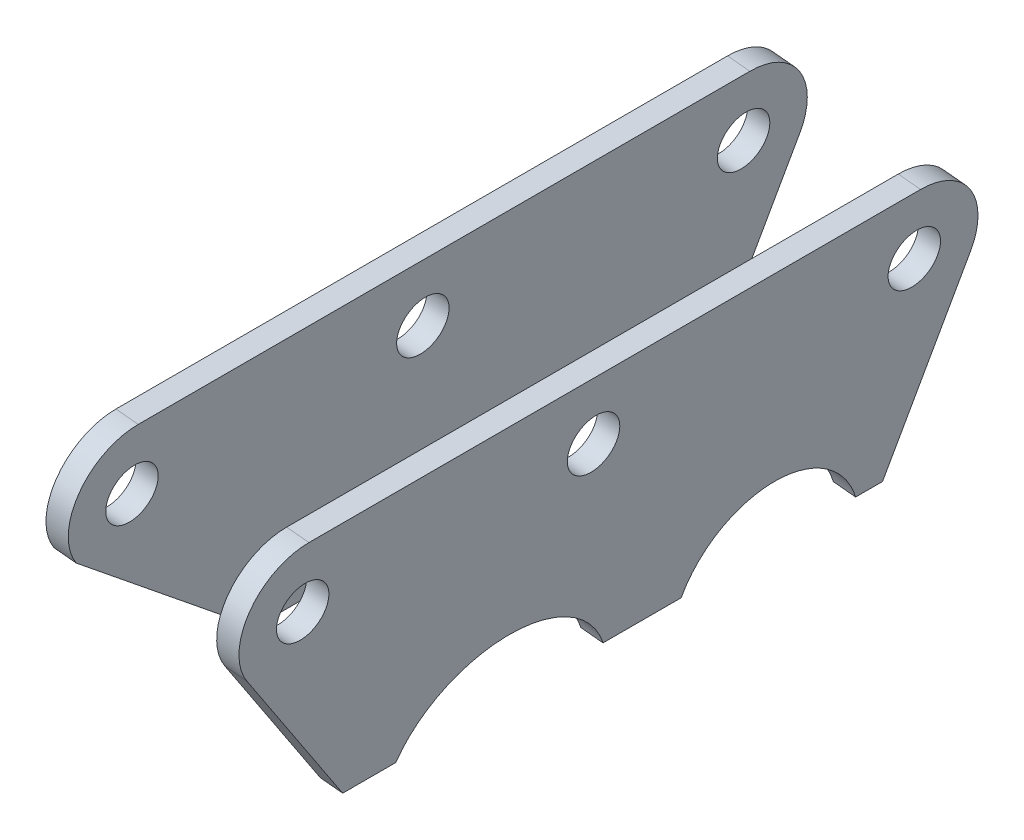
SolidWorks part; units mm, degrees
material "1.0545 (S355N)"
ref_plane "Płaszczyzna XY" through (0, 0, 0) normal (0, 0, 1) x (1, 0, 0)
ref_plane "Płaszczyzna XZ" through (0, 0, 0) normal (0, 1, 0) x (1, 0, 0)
ref_plane "Płaszczyzna YZ" through (0, 0, 0) normal (1, 0, 0) x (0, 0, -1)
ref_plane "Płaszczyzna1" through (1510.2654, -150.1623, 0) normal (0.9951, -0.0989, 0) x (0, 0, -1)
sketch "Szkic1" plane through (1510.2654, -150.1623, 0) normal (0.9951, -0.0989, 0) x (0, 0, -1)
  line L0 (-176, 389.2443) -> (-94, 389.2443)
  line L1 (-182.9922, 375.9111) -> (-168.0155, 354.2443)
  line L2 (-86.13, 377.5329) -> (-95.6331, 354.2443)
  line L3 (-133.1104, 354.2443) -> (-122.6322, 354.2443)
  line L4 (-168.0155, 354.2443) -> (-160.8854, 354.2443)
  line L5 (-133.1104, 354.2443) -> (-122.6322, 354.2443)
  line L6 (-99.2442, 354.2443) -> (-95.6331, 354.2443)
  circle A3 centre (-176, 380.7443) radius 3.5
  circle A4 centre (-137, 380.7443) radius 3.5
  circle A5 centre (-94, 380.7443) radius 3.5
  arc A6 (-86.13, 377.5329) -> (-94, 389.2443) centre (-94, 380.7443) ccw
  arc A7 (-176, 389.2443) -> (-182.9922, 375.9111) centre (-176, 380.7443) ccw
  circle A8 centre (-176, 380.7443) radius 8.5 construction
  circle A9 centre (-94, 380.7443) radius 8.5 construction
  spline S1 degree 3 poles (-162.0456, 347.4683) (-165.8972, 372.1699) (-136.379, 376.7725) (-132.5274, 352.071) (-128.6758, 327.3695) (-158.194, 322.7668) (-162.0456, 347.4683) (-165.8972, 372.1699) (-136.379, 376.7725) knots -0.5 0 0 0 0.5 0.5 0.5 1 1 1 1.5 1.5 1.5 weights 1 0.333333 0.333333 1 0.333333 0.333333 1 0.333333 0.333333 only from (-162.0456, 347.4683) to (-162.0456, 347.4683)
  spline S3 degree 3 poles (-105.4876, 361.0949) (-82.9777, 350.2182) (-93.9223, 327.5677) (-116.4323, 338.4444) (-138.9422, 349.3211) (-127.9975, 371.9716) (-105.4876, 361.0949) (-82.9777, 350.2182) (-93.9223, 327.5677) knots -0.5 0 0 0 0.5 0.5 0.5 1 1 1 1.5 1.5 1.5 weights 1 0.333333 0.333333 1 0.333333 0.333333 1 0.333333 0.333333 only from (-105.4876, 361.0949) to (-105.4876, 361.0949)
  dimension "D1" = 7
  dimension "D2" = 5
  dimension "D3" = 35
extrude "Dodanie-wyciągnięcie1" add sketch "Szkic1" against normal blind 3 contours L3 S3 L6 L2 A6 L0 A7 L1 L4 S1 A3 A4 A5
ref_plane "Płaszczyzna2" through (1487.3783, -147.8867, 0) normal (0.9951, -0.0989, 0) x (0, 0, -1)
sketch "Szkic2" plane through (1487.3783, -147.8867, 0) normal (0.9951, -0.0989, 0) x (0, 0, -1)
  line L0 (-176, 389.2443) -> (-94, 389.2443) construction
  line L1 (-176, 389.2443) -> (-94, 389.2443)
  line L2 (-86.13, 377.5329) -> (-95.6331, 354.2443)
  line L3 (-156.8404, 354.2443) -> (-182.9922, 375.9111)
  line L4 (-156.8404, 354.2443) -> (-146.9214, 354.2443)
  line L5 (-95.6331, 354.2443) -> (-97.5004, 354.2443)
  line L6 (-133.1104, 354.2443) -> (-122.6322, 354.2443) construction
  circle A0 centre (-176, 380.7443) radius 3.5 construction
  circle A1 centre (-176, 380.7443) radius 3.5
  circle A2 centre (-176, 380.7443) radius 3.5 construction
  circle A3 centre (-137, 380.7443) radius 3.5 construction
  circle A4 centre (-94, 380.7443) radius 3.5 construction
  circle A5 centre (-176, 380.7443) radius 3.5
  circle A6 centre (-137, 380.7443) radius 3.5
  circle A7 centre (-94, 380.7443) radius 3.5
  arc A8 (-86.13, 377.5329) -> (-94, 389.2443) centre (-94, 380.7443) ccw construction
  arc A9 (-176, 389.2443) -> (-182.9922, 375.9111) centre (-176, 380.7443) ccw construction
  arc A10 (-86.13, 377.5329) -> (-94, 389.2443) centre (-94, 380.7443) ccw
  arc A11 (-176, 389.2443) -> (-182.9922, 375.9111) centre (-176, 380.7443) ccw
  spline S1 degree 3 poles (-120.3805, 345.2638) (-130.8796, 332.6113) (-147.7816, 336.6805) (-147.2977, 351.7442) (-146.8138, 366.8079) (-129.6251, 371.6646) (-119.9239, 359.4787) knots 0 0 0 0 0.5 0.5 0.5 1 1 1 1 weights 1 0.530848 0.530848 1 0.530848 0.530848 1
  spline S3 degree 3 poles (-104.3675, 363.4132) (-81.8575, 352.5364) (-92.8022, 329.8859) (-115.3121, 340.7626) (-137.822, 351.6393) (-126.8774, 374.2899) (-104.3675, 363.4132) (-81.8575, 352.5364) (-92.8022, 329.8859) knots -0.5 0 0 0 0.5 0.5 0.5 1 1 1 1.5 1.5 1.5 weights 1 0.333333 0.333333 1 0.333333 0.333333 1 0.333333 0.333333 only from (-104.3675, 363.4132) to (-104.3675, 363.4132)
extrude "Dodanie-wyciągnięcie2" add sketch "Szkic2" against normal blind 3 separate body contours S1 S3 L5 L2 A10 L1 A11 L3 L4 A1 A6 A7
